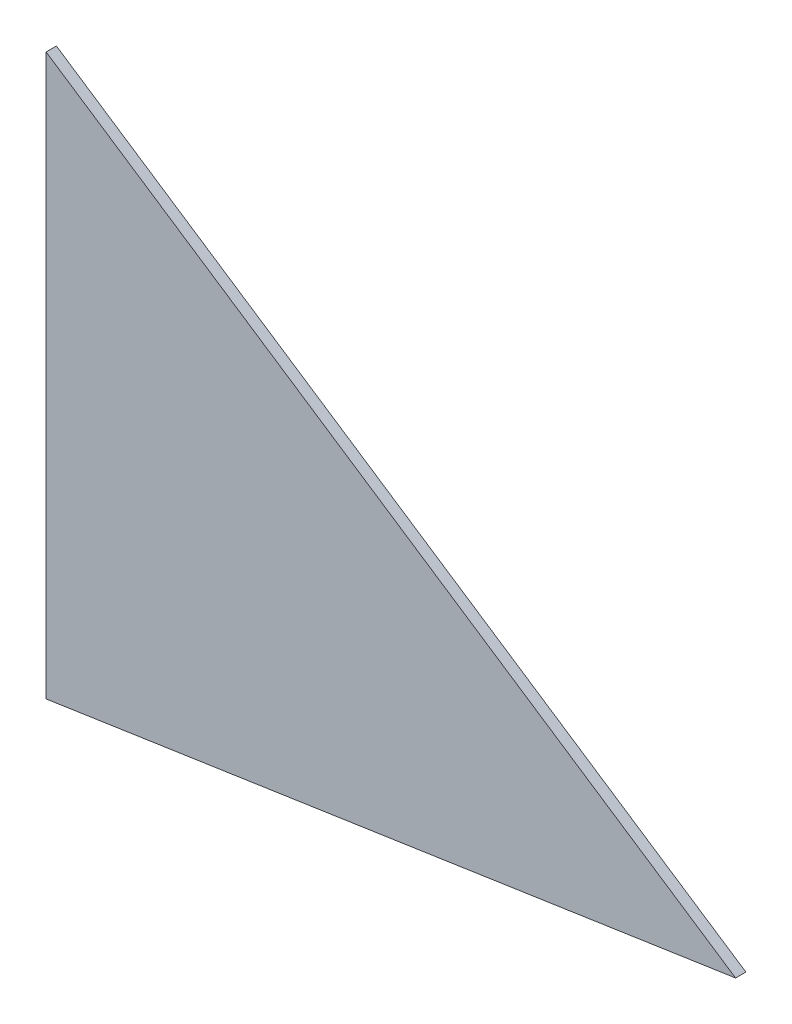
SolidWorks part; units mm, degrees
material "Stop 1060"
ref_plane "Front Plane" through (0, 0, 0) normal (0, 0, 1) x (1, 0, 0)
ref_plane "Top Plane" through (0, 0, 0) normal (0, 1, 0) x (1, 0, 0)
ref_plane "Right Plane" through (0, 0, 0) normal (1, 0, 0) x (0, 0, -1)
sketch "Szkic1" plane through (0, 0, 0) normal (0, 0, 1) x (1, 0, 0)
  line L6 (-233.8753, -176.8408) -> (-903.9239, -277.0091)
  line L7 (-233.8753, -176.8408) -> (-903.9239, 267.5253)
  line L8 (-903.9239, 267.5253) -> (-903.9239, -277.0091)
extrude "Dodanie-wyciągnięcie1" add sketch "Szkic1" along normal blind 10 contours L8 L6 L7
